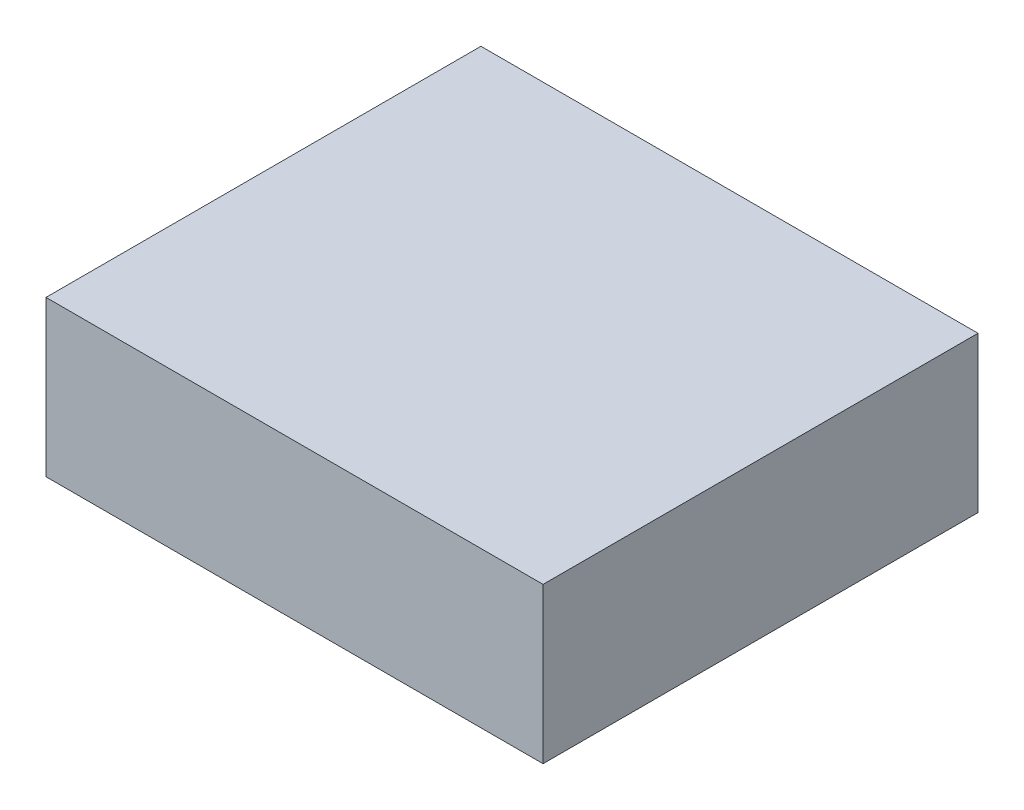
SolidWorks part; units mm, degrees
material "ABS"
ref_plane "Front Plane" through (0, 0, 0) normal (0, 0, 1) x (1, 0, 0)
ref_plane "Top Plane" through (0, 0, 0) normal (0, 1, 0) x (1, 0, 0)
ref_plane "Right Plane" through (0, 0, 0) normal (1, 0, 0) x (0, 0, -1)
sketch "Sketch1" plane through (0, 0, 0) normal (0, 0, 1) x (1, 0, 0)
  line L0 (-5.08, 0) -> (5.08, 0)
  line L1 (5.08, 0) -> (5.08, -3.175)
  line L2 (5.08, -3.175) -> (-5.08, -3.175)
  line L3 (-5.08, -3.175) -> (-5.08, 0)
  point P3 (0, -3.175)
  dimension "D1" = 10.16
  dimension "D2" = 3.175
extrude "Boss-Extrude1" add sketch "Sketch1" along normal mid plane 8.89
sketch "Sketch2" plane through (0, 0, 0) normal (0, 0, 1) x (1, 0, 0)
  line L0 (-1.27, 2.54) -> (-1.27, 3.3867)
  line L1 (1.27, 2.54) -> (1.27, 3.3867)
  line L2 (-2.3947, 3.3867) -> (-1.27, 3.3867)
  line L3 (1.27, 3.3867) -> (2.3947, 3.3867)
  line L4 (-1.27, 0.3403) -> (-1.27, 0)
  line L5 (5.08, 0) -> (-5.08, 0) construction
  line L6 (1.27, 0.3403) -> (1.27, 0)
  line L7 (-1.27, 0) -> (1.27, 0)
  arc A0 (-2.3947, 3.3867) -> (-1.27, 0.3403) centre (0, 2.54) ccw
  arc A1 (-1.27, 2.54) -> (1.27, 2.54) centre (0, 2.54) ccw
  arc A2 (1.27, 0.3403) -> (2.3947, 3.3867) centre (0, 2.54) ccw
  dimension "D1" = 5.08
  dimension "D2" = 2.54
extrude "Boss-Extrude2" [suppressed] add sketch "Sketch2" along normal mid plane 3.81
sketch "Sketch3" plane through (0, -3.175, 0) normal (0, -1, 0) x (1, 0, 0)
  line L0 (-2.54, 2.54) -> (-2.54, -2.54)
  line L1 (-2.54, -2.54) -> (2.54, -2.54)
  line L2 (2.54, -2.54) -> (2.54, 2.54)
  line L3 (2.54, 2.54) -> (-2.54, 2.54)
  line L4 (-5.08, -4.445) -> (5.08, -4.445)
  line L5 (5.08, -4.445) -> (5.08, 4.445)
  line L6 (5.08, 4.445) -> (-5.08, 4.445)
  line L7 (-5.08, 4.445) -> (-5.08, -4.445)
  line L8 (-5.08, -4.445) -> (5.08, -4.445)
  line L9 (5.08, -4.445) -> (5.08, 4.445)
  line L10 (5.08, 4.445) -> (-5.08, 4.445)
  line L11 (-5.08, 4.445) -> (-5.08, -4.445)
  dimension "D1" = 0
extrude "Cut-Extrude1" cut sketch "Sketch3" against normal blind 1.905 flip side to cut
